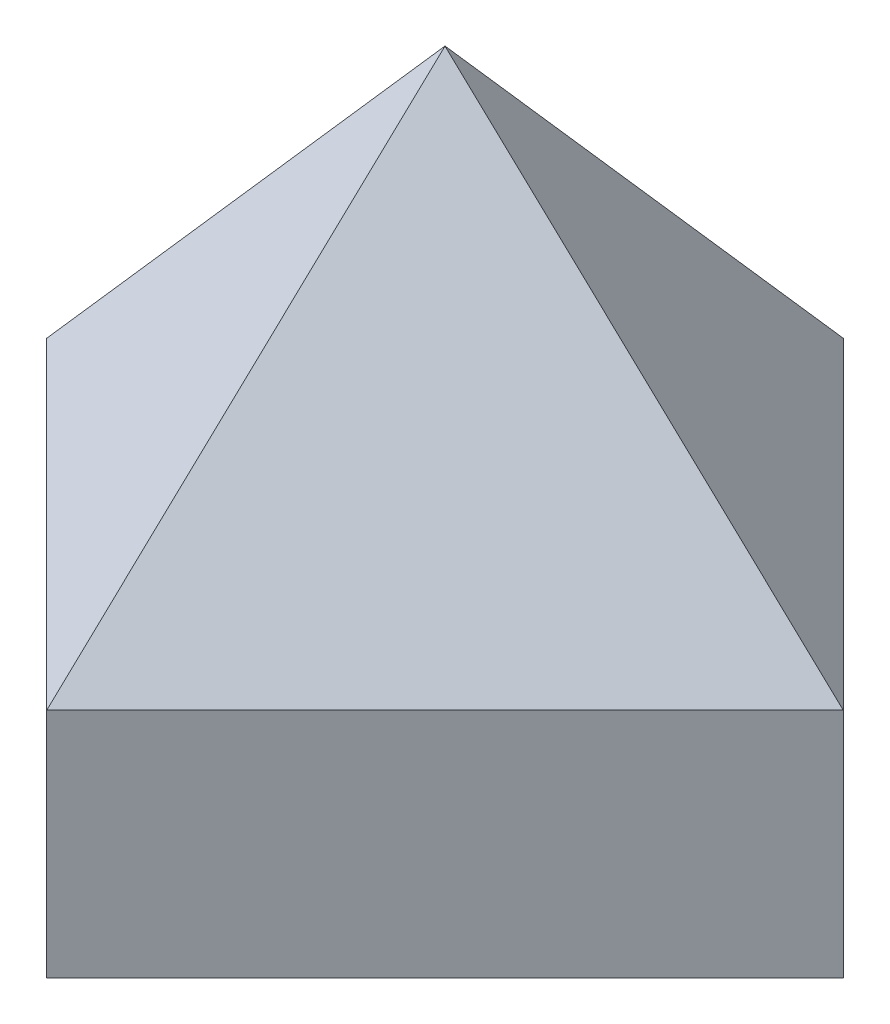
SolidWorks part; units mm, degrees
ref_plane "Front" through (0, 0, 0) normal (0, 0, 1) x (1, 0, 0)
ref_plane "Top" through (0, 0, 0) normal (0, 1, 0) x (1, 0, 0)
ref_plane "Right" through (0, 0, 0) normal (1, 0, 0) x (0, 0, -1)
sketch "Sketch1" plane through (0, 0, 0) normal (0, 1, 0) x (1, 0, 0)
  line L0 (-35.5279, -10) -> (3.3629, -48.8909)
  line L1 (3.3629, -48.8909) -> (-44.7203, -96.9741)
  line L2 (-44.7203, -96.9741) -> (-83.6112, -58.0833)
  line L3 (-83.6112, -58.0833) -> (-35.5279, -10)
  dimension "D1" = 68
  dimension "D2" = 55
  dimension "D3" = 10
extrude "Extrude1" add sketch "Sketch1" along normal blind 28
sketch "Sketch2" plane through (0, 28, 0) normal (0, 1, 0) x (-1, 0, 0)
  line L0 (35.5279, 10) -> (-3.3629, 48.8909)
  line L1 (-3.3629, 48.8909) -> (44.7203, 96.9741)
  line L2 (44.7203, 96.9741) -> (83.6112, 58.0833)
  line L3 (83.6112, 58.0833) -> (35.5279, 10)
  line L4 (35.5279, 10) -> (44.7203, 96.9741) construction
  point P2 (40.1241, 53.4871)
ref_plane "Plane1" through (0, 0, 53.4871) normal (0, 0, 1) x (1, 0, 0)
sketch "Sketch3" plane through (0, 0, 53.4871) normal (0, 0, 1) x (1, 0, 0)
  point P0 (-40.1241, 78)
  dimension "D1" = 50
loft "Loft1" add profiles "Sketch3", "Sketch2"
sketch "Sketch4" plane through (0, 0, 0) normal (0, 0, 1) x (1, 0, 0)
  line L0 (-40.1241, 78) -> (45.3629, 0)
  line L1 (45.3629, 0) -> (30.7534, 0) construction
  line L2 (3.3629, 28) -> (3.3629, 0) construction
  dimension "D1" = 42
sketch "Sketch5" plane through (0, 0, 0) normal (0, 1, 0) x (1, 0, 0)
  line L0 (45.3629, 0) -> (3.0827, -73.2315)
  line L1 (45.3629, 0) -> (30.7534, 0) construction
  line L2 (-40.1241, 0) -> (45.3629, 0) construction
  dimension "D1" = 60
ref_plane "Cutting Plane" through (17.898, 19.616, 10.3334) normal (-0.6281, -0.6884, -0.3627) x (0.7781, -0.5557, -0.2928)
